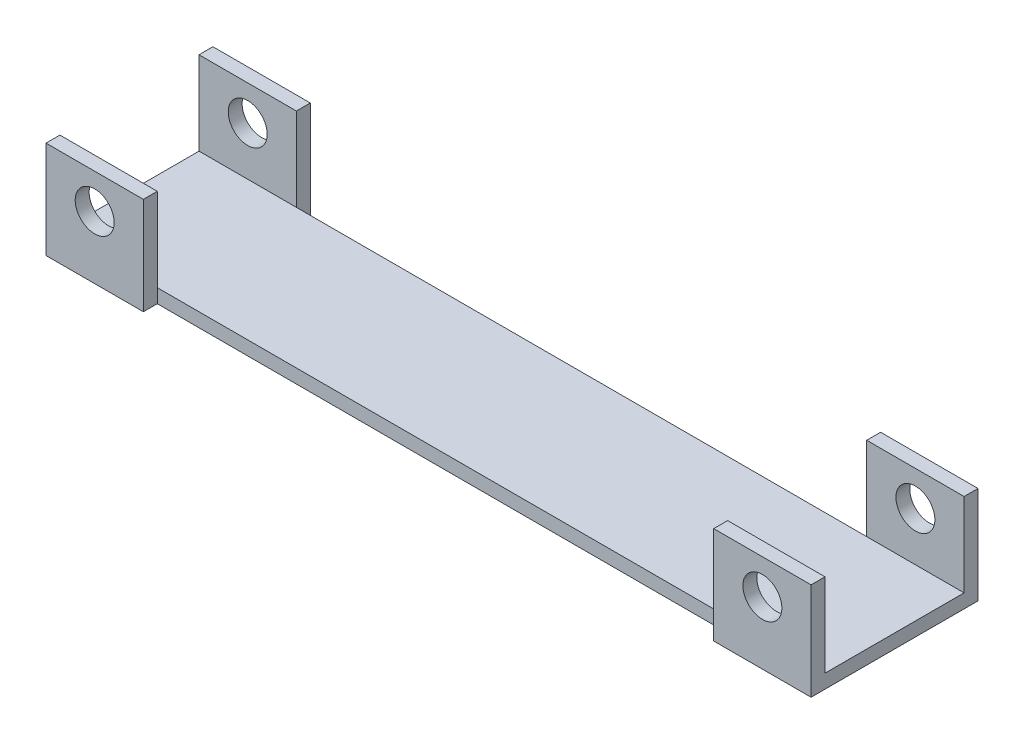
SolidWorks part; units mm, degrees
ref_plane "Płaszczyzna przednia" through (0, 0, 0) normal (0, 0, 1) x (1, 0, 0)
ref_plane "Płaszczyzna górna" through (0, 0, 0) normal (0, 1, 0) x (1, 0, 0)
ref_plane "Płaszczyzna prawa" through (0, 0, 0) normal (1, 0, 0) x (0, 0, -1)
sketch "Szkic1" plane through (0, 0, 0) normal (0, 1, 0) x (1, 0, 0)
  line L1 (0, 0) -> (275, 0)
  line L2 (0, 0) -> (0, 50)
  line L3 (0, 50) -> (275, 50)
  line L4 (275, 0) -> (275, 50)
  dimension "D1" = 275
  dimension "D2" = 50
extrude "Dodanie-wyciągnięcie1" add sketch "Szkic1" along normal blind 5
sketch "Szkic2" plane through (0, 0, 0) normal (0, 0, 1) x (1, 0, 0)
  line L0 (0, 0) -> (275, 0) construction
  line L1 (0, 0) -> (35, 0)
  line L2 (0, 0) -> (0, 35)
  line L3 (0, 35) -> (35, 35)
  line L4 (35, 0) -> (35, 35)
  line L5 (275, 5) -> (275, 0) construction
  line L6 (137.5, 0) -> (137.5, 40) construction
  line L7 (240, 0) -> (240, 35)
  line L8 (275, 35) -> (240, 35)
  line L9 (275, 0) -> (275, 35)
  line L10 (275, 0) -> (240, 0)
  circle A0 centre (17.5, 22.5) radius 7
  circle A1 centre (257.5, 22.5) radius 7
  point P8 (17.5, 35)
  dimension "D4" = 14
  dimension "D1" = 35
  dimension "D2" = 35
  dimension "D5" = 22.5
extrude "Dodanie-wyciągnięcie2" add sketch "Szkic2" along normal blind 5
ref_plane "Płaszczyzna lustra" through (0, 0, -25) normal (0, 0, -1) x (-1, 0, 0)
mirror "Lustro1" about plane through (0, 0, -25) normal (0, 0, -1) of "Dodanie-wyciągnięcie2"
